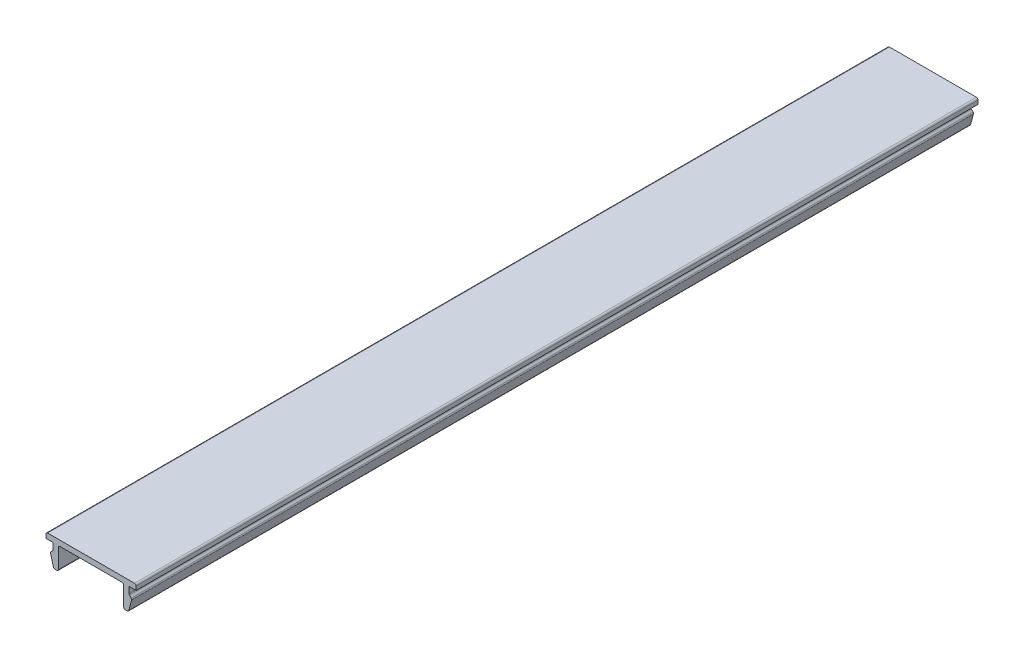
SolidWorks part; units mm, degrees
material "ABS"
ref_plane "Plano frontal" through (0, 0, 0) normal (0, 0, 1) x (1, 0, 0)
ref_plane "Plano superior" through (0, 0, 0) normal (0, 1, 0) x (1, 0, 0)
ref_plane "Plano direito" through (0, 0, 0) normal (1, 0, 0) x (0, 0, -1)
sketch "Sketch1" plane through (0, 0, 0) normal (0, 0, 1) x (1, 0, 0)
  line L0 (-8.3, 1) -> (8.3, 1)
  line L1 (-8.3, 0) -> (-7, 0)
  line L2 (-8.3, 1) -> (-8.3, 0)
  line L3 (8.3, 1) -> (8.3, 0)
  line L4 (-7, 0) -> (-7, -1.3)
  line L5 (-7, -1.3) -> (-7.5, -1.8)
  line L6 (-7.5, -1.8) -> (-6.8837, -4.1)
  line L7 (-6, 0) -> (-6, -4.1)
  line L8 (-6, -4.1) -> (-6.8837, -4.1)
  line L9 (0, 0) -> (0, -1.7195) construction
  line L10 (6, -4.1) -> (6.8837, -4.1)
  line L11 (6, 0) -> (6, -4.1)
  line L12 (7.5, -1.8) -> (6.8837, -4.1)
  line L13 (7, -1.3) -> (7.5, -1.8)
  line L14 (7, 0) -> (7, -1.3)
  line L15 (7, 0) -> (8.3, 0)
  line L16 (-8.3, 0) -> (8.3, 0) construction
  line L17 (-6, 0) -> (6, 0)
  point P21 (0, 1)
  dimension "D1" = 16.6
  dimension "D3" = 1.3
  dimension "D4" = 1.3
  dimension "D5" = 135
  dimension "D6" = 120
  dimension "D7" = 4.1
  dimension "D8" = 0.5
  dimension "D9" = 1
  dimension "D2" = 1
extrude "Boss-Extrude1" add sketch "Sketch1" along normal blind 155
fillet "Fillet1" radius 0.3 12 edges at (8.3, 1, 77.5) (7, -1.3, 77.5) (7.5, -1.8, 77.5) (6.8837, -4.1, 77.5) (6, -4.1, 77.5) (6, 0, 77.5) (-6, 0, 77.5) (-6, -4.1, 77.5) (-6.8837, -4.1, 77.5) (-7.5, -1.8, 77.5) (-7, -1.3, 77.5) (-8.3, 1, 77.5)
